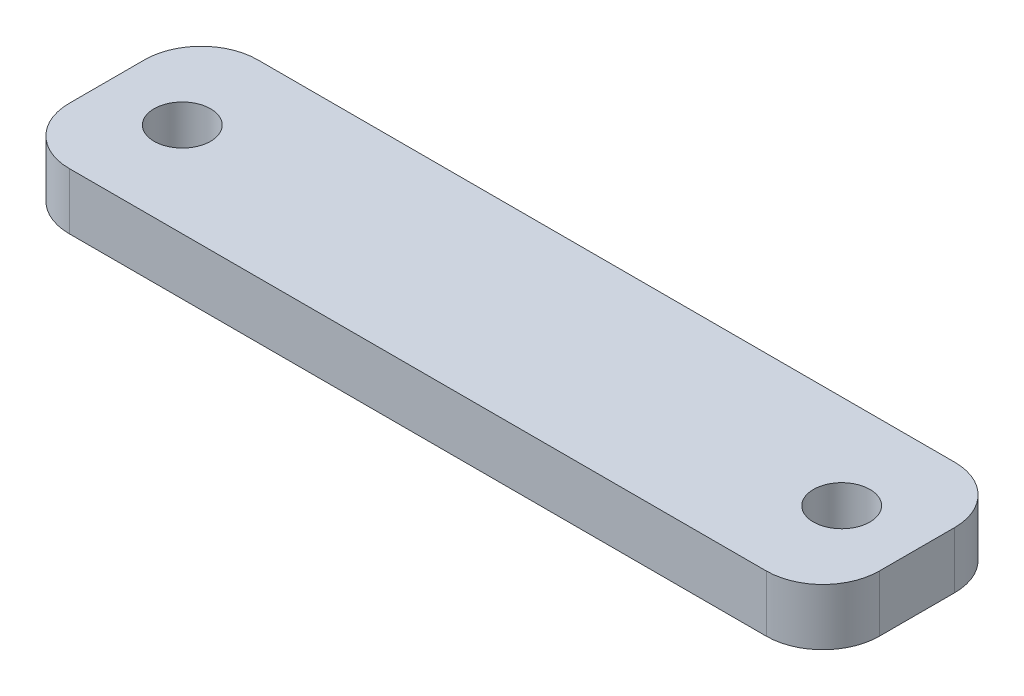
SolidWorks part; units mm, degrees
ref_plane "Front Plane" through (0, 0, 0) normal (0, 0, 1) x (1, 0, 0)
ref_plane "Top Plane" through (0, 0, 0) normal (0, 1, 0) x (1, 0, 0)
ref_plane "Right Plane" through (0, 0, 0) normal (1, 0, 0) x (0, 0, -1)
sketch "Sketch1" plane through (0, 0, 0) normal (0, 1, 0) x (1, 0, 0)
  line L1 (-21.5, 5) -> (21.5, 5)
  line L2 (-21.5, 5) -> (-21.5, -5)
  line L3 (-21.5, -5) -> (21.5, -5)
  line L4 (21.5, 5) -> (21.5, -5)
  line L5 (-21.5, 5) -> (21.5, -5) construction
  line L6 (-21.5, -5) -> (21.5, 5) construction
  point P0 (0, 0)
  dimension "D1" = 10
  dimension "D2" = 43
extrude "Boss-Extrude1" add sketch "Sketch1" along normal blind 3
sketch "Sketch2" plane through (0, 3, 0) normal (0, 1, 0) x (1, 0, 0)
  point P10 (26.3156, 0)
fillet "Fillet1" radius 3 4 edges at (21.5, 1.5, 5) (21.5, 1.5, -5) (-21.5, 1.5, 5) (-21.5, 1.5, -5)
hole_wizard "Ø3.0mm Dowel Hole1" positions "Sketch5" profile "Sketch6" hole size "Ø3.0" standard "ISO" end condition through all
sketch "Sketch5" plane through (0, 0, 0) normal (0, -1, 0) x (-1, 0, 0)
  line L1 (-21.5, -2) -> (-21.5, 2) construction
  line L3 (21.5, 0) -> (-21.5, 0) construction
  line L4 (21.5, 2) -> (21.5, -2) construction
  line L5 (21.5, 2) -> (21.5, -2) construction
  point P0 (-17.5, 0)
  point P2 (17.5, 0)
  dimension "D1" = 4
  dimension "D2" = 35
sketch "Sketch6" plane through (17.5, 0, 0) normal (1, 0, 0) x (0, 0, -1)
  line L0 (0, 0) -> (0, 3)
  line L1 (0, 3) -> (1.5, 3)
  line L2 (1.5, 3) -> (1.5, 0)
  line L5 (1.5, 0) -> (0, 0)
  line L11 (0, -6.35) -> (0, 107.95) construction
  dimension "Thru Hole Dia." = 3
  dimension "Thru Hole Depth" = 3
equation "\"globalength1\"=55"
